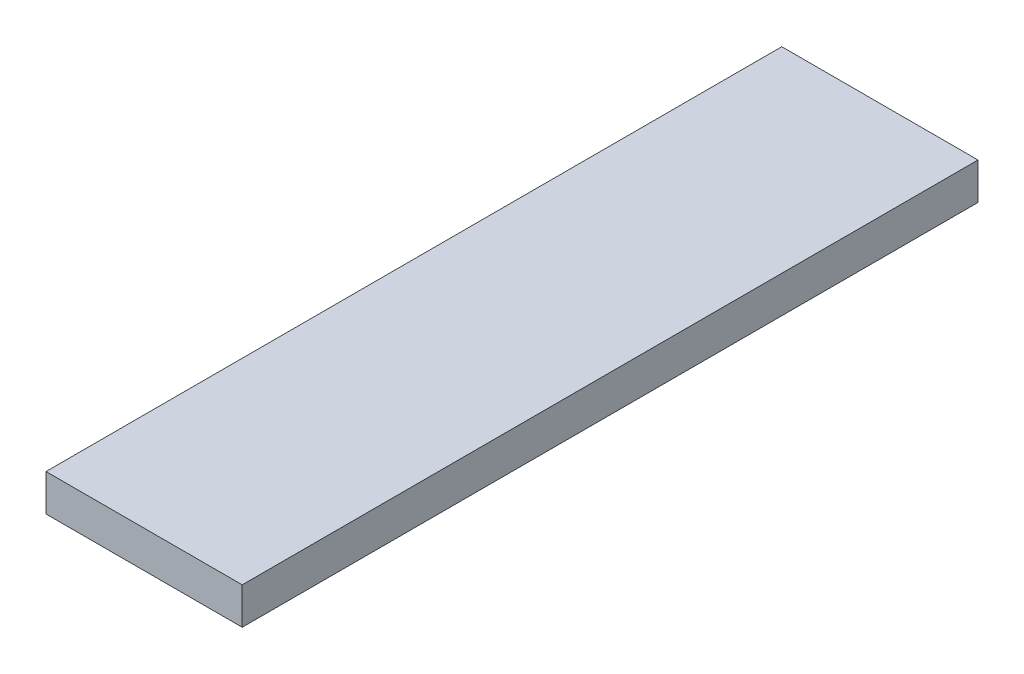
SolidWorks part; units mm, degrees
material "橡胶"
ref_plane "前视基准面" through (0, 0, 0) normal (0, 0, 1) x (1, 0, 0)
ref_plane "上视基准面" through (0, 0, 0) normal (0, 1, 0) x (1, 0, 0)
ref_plane "右视基准面" through (0, 0, 0) normal (1, 0, 0) x (0, 0, -1)
sketch "草图1" plane through (0, 0, 0) normal (0, 1, 0) x (1, 0, 0)
  line L1 (-8, 30) -> (8, 30)
  line L2 (-8, 30) -> (-8, -30)
  line L3 (-8, -30) -> (8, -30)
  line L4 (8, 30) -> (8, -30)
  line L5 (-8, 30) -> (8, -30) construction
  line L6 (-8, -30) -> (8, 30) construction
  point P0 (0, 0)
  dimension "D1" = 16
  dimension "D2" = 60
extrude "凸台-拉伸1" add sketch "草图1" along normal blind 3
sketch "草图2" plane through (0, 3, 0) normal (0, 1, 0) x (1, 0, 0)
  circle A0 centre (0, 0) radius 3.3649
